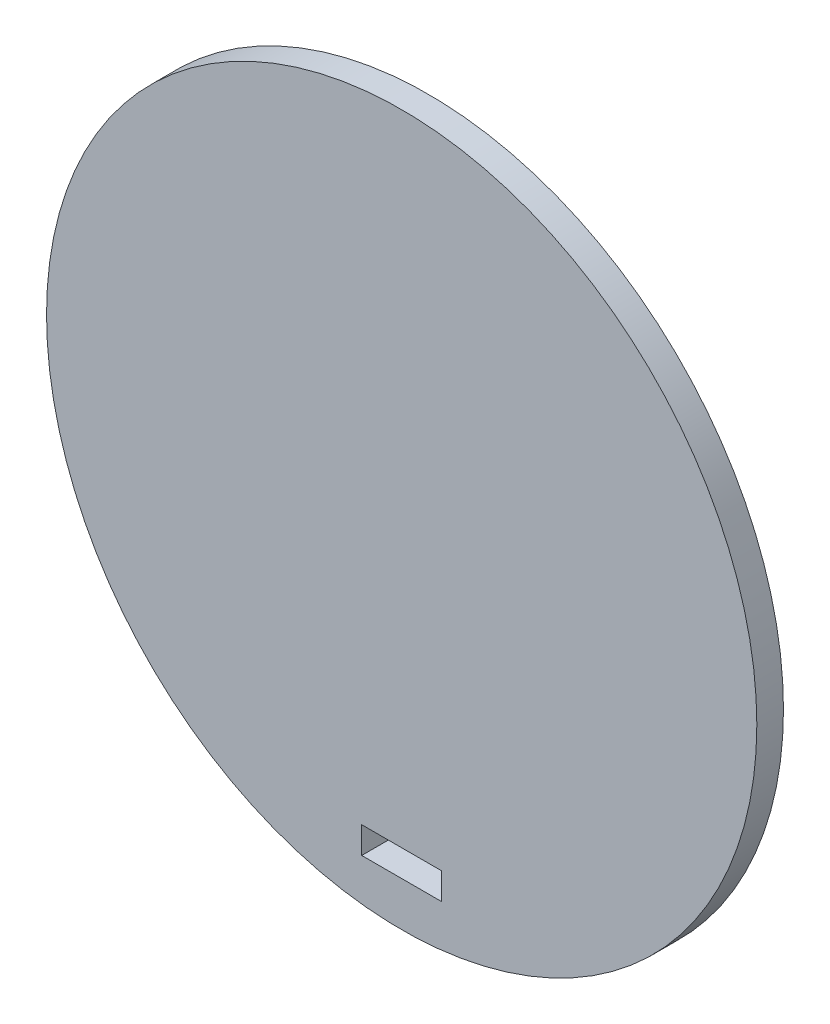
SolidWorks part; units mm, degrees
ref_plane "Front Plane" through (0, 0, 0) normal (0, 0, 1) x (1, 0, 0)
ref_plane "Top Plane" through (0, 0, 0) normal (0, 1, 0) x (1, 0, 0)
ref_plane "Right Plane" through (0, 0, 0) normal (1, 0, 0) x (0, 0, -1)
sketch "Sketch1" plane through (0, 0, 0) normal (0, 0, 1) x (1, 0, 0)
  circle A0 centre (0, 0) radius 40
extrude "Boss-Extrude1" add sketch "Sketch1" along normal blind 3
sketch "Sketch2" plane through (0, 0, 0) normal (0, 0, -1) x (-1, 0, 0)
  line L0 (0, 0) -> (0, -40) construction
  line L1 (0, -40) -> (0, -35)
  line L2 (0, -35) -> (4.5, -35)
  line L3 (4.5, -35) -> (4.5, -32)
  line L4 (0, -35) -> (-4.5, -35)
  line L5 (-4.5, -35) -> (-4.5, -32)
  line L6 (-4.5, -32) -> (4.5, -32)
  circle A0 centre (0, 0) radius 40 construction
extrude "Cut-Extrude1" cut sketch "Sketch2" against normal blind 3 contours L6 L0 L2 L3 | L0 L6 L5 L4
